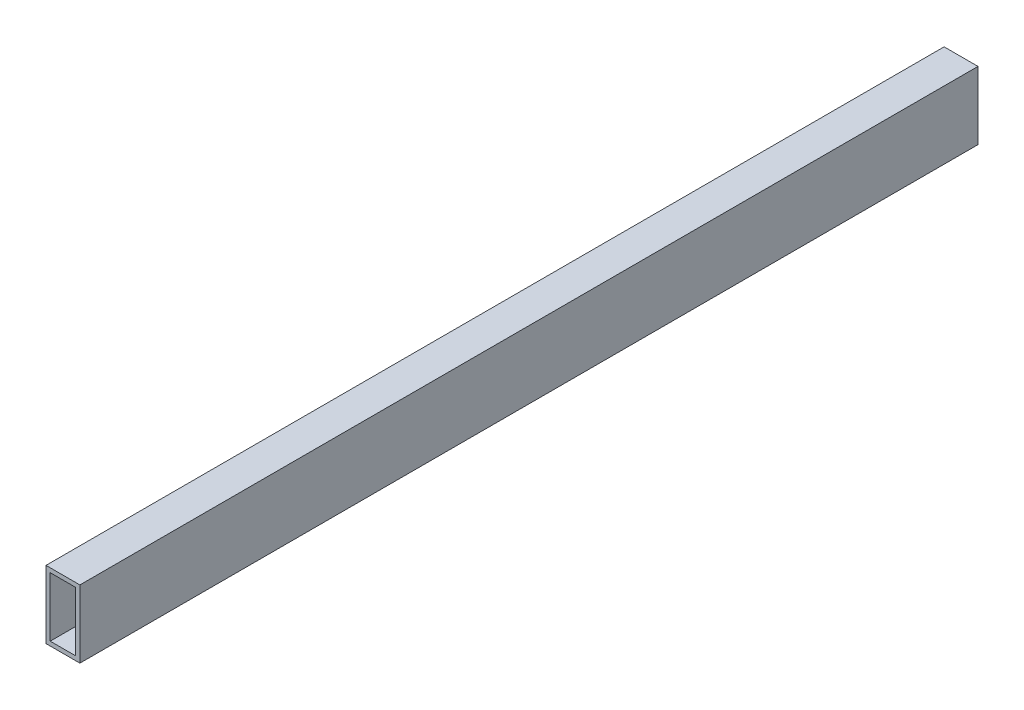
SolidWorks part; units mm, degrees
ref_plane "Front Plane" through (0, 0, 0) normal (0, 0, 1) x (1, 0, 0)
ref_plane "Top Plane" through (0, 0, 0) normal (0, 1, 0) x (1, 0, 0)
ref_plane "Right Plane" through (0, 0, 0) normal (1, 0, 0) x (0, 0, -1)
sketch "Sketch1" plane through (0, 0, 0) normal (0, 0, 1) x (1, 0, 0)
  line L1 (-12.7, -25.4) -> (12.7, -25.4)
  line L2 (-12.7, -25.4) -> (-12.7, 25.4)
  line L3 (-12.7, 25.4) -> (12.7, 25.4)
  line L4 (12.7, -25.4) -> (12.7, 25.4)
  line L5 (-12.7, -25.4) -> (12.7, 25.4) construction
  line L6 (-12.7, 25.4) -> (12.7, -25.4) construction
  line L7 (-9.525, -22.225) -> (9.525, -22.225)
  line L8 (-9.525, -22.225) -> (-9.525, 22.225)
  line L9 (-9.525, 22.225) -> (9.525, 22.225)
  line L10 (9.525, -22.225) -> (9.525, 22.225)
  line L11 (-9.525, -22.225) -> (9.525, 22.225) construction
  line L12 (-9.525, 22.225) -> (9.525, -22.225) construction
  point P0 (0, 0)
  point P6 (0, 0)
  dimension "D1" = 50.8
  dimension "D2" = 25.4
  dimension "D3" = 3.175
  dimension "D4" = 3.175
extrude "Boss-Extrude1" add sketch "Sketch1" along normal blind 673.1
